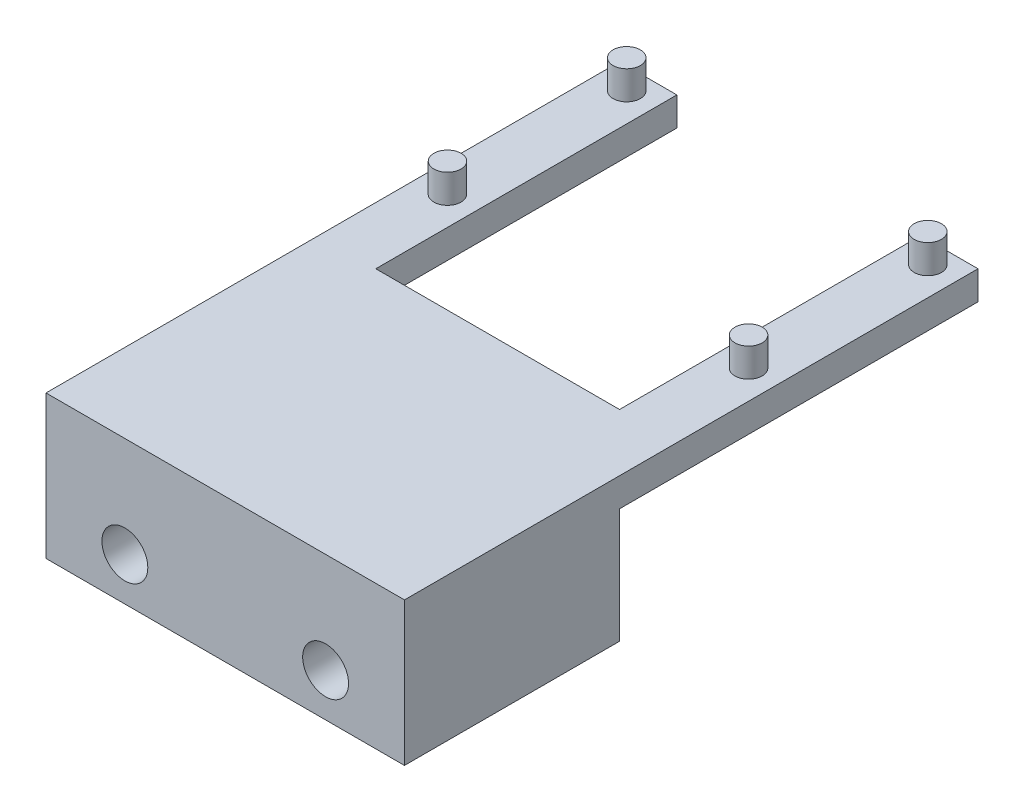
SolidWorks part; units mm, degrees
ref_plane "Front Plane" through (0, 0, 0) normal (0, 0, 1) x (1, 0, 0)
ref_plane "Top Plane" through (0, 0, 0) normal (0, 1, 0) x (1, 0, 0)
ref_plane "Right Plane" through (0, 0, 0) normal (1, 0, 0) x (0, 0, -1)
sketch "Sketch1" plane through (0, 0, 0) normal (0, 1, 0) x (1, 0, 0)
  line L0 (-8.5, 12.5) -> (-8.5, -8.5)
  line L1 (-12.5, 12.5) -> (-8.5, 12.5)
  line L2 (-12.5, 12.5) -> (-12.5, -12.5)
  line L3 (-12.5, -12.5) -> (12.5, -12.5)
  line L4 (12.5, 12.5) -> (12.5, -12.5)
  line L5 (-12.5, 12.5) -> (12.5, -12.5) construction
  line L6 (-12.5, -12.5) -> (12.5, 12.5) construction
  line L7 (-8.5, -8.5) -> (8.5, -8.5)
  line L8 (8.5, -8.5) -> (8.5, 12.5)
  line L9 (8.5, 12.5) -> (12.5, 12.5)
  point P0 (0, 0)
  point P18 (11.1507, 11.1507)
  point P19 (10, 10)
  point P20 (10, 11)
  point P21 (0, 0)
  point P22 (-10.5, -5.5389)
  point P23 (10.5, -1.5)
  dimension "D1" = 25
  dimension "D2" = 25
  dimension "D7" = 4
  dimension "D8" = 4
  dimension "D9" = 4
extrude "Boss-Extrude1" add sketch "Sketch1" along normal blind 2
sketch "Sketch2" plane through (0, 2, 0) normal (0, 1, 0) x (1, 0, 0)
  circle A3 centre (-10.5, 11) radius 0.95
  circle A4 centre (-10.5, -1.5) radius 0.95
  circle A5 centre (10.5, 11) radius 0.95
  circle A6 centre (10.5, -1.5) radius 0.95
  point P8 (-10.5, 11)
  point P12 (-10.5, -1.5)
  point P16 (10.5, 11)
  point P20 (10.5, -1.5)
  dimension "D1" = 21
  dimension "D2" = 12.5
extrude "Boss-Extrude2" add sketch "Sketch2" along normal blind 2
sketch "Sketch3" plane through (0, 0, 12.5) normal (0, 0, 1) x (1, 0, 0)
  line L0 (-12.5, 2) -> (-12.5, 0) construction
  line L1 (-12.5, 2) -> (12.5, 2)
  line L2 (-12.5, 2) -> (-12.5, -8)
  line L3 (-12.5, -8) -> (12.5, -8)
  line L4 (12.5, 2) -> (12.5, -8)
  line L5 (12.5, 2) -> (12.5, 0) construction
  line L6 (-12.5, 2) -> (12.5, 2) construction
  dimension "D1" = 0
  dimension "D2" = 0
  dimension "D3" = 0
  dimension "D4" = 10
extrude "Boss-Extrude3" add sketch "Sketch3" along normal blind 15
sketch "Sketch4" plane through (0, 0, 27.5) normal (0, 0, 1) x (1, 0, 0)
  line L0 (-12.5, -8) -> (12.5, -8) construction
  line L3 (-12.5, 2) -> (-12.5, -8) construction
  circle A0 centre (-7, -5) radius 1.6
  circle A1 centre (7, -5) radius 1.6
  point P6 (6.2506, -4)
  point P7 (7, -5)
  dimension "D1" = 14
  dimension "D2" = 3
  dimension "D3" = 5.5
extrude "Cut-Extrude1" cut sketch "Sketch4" against normal blind 20
